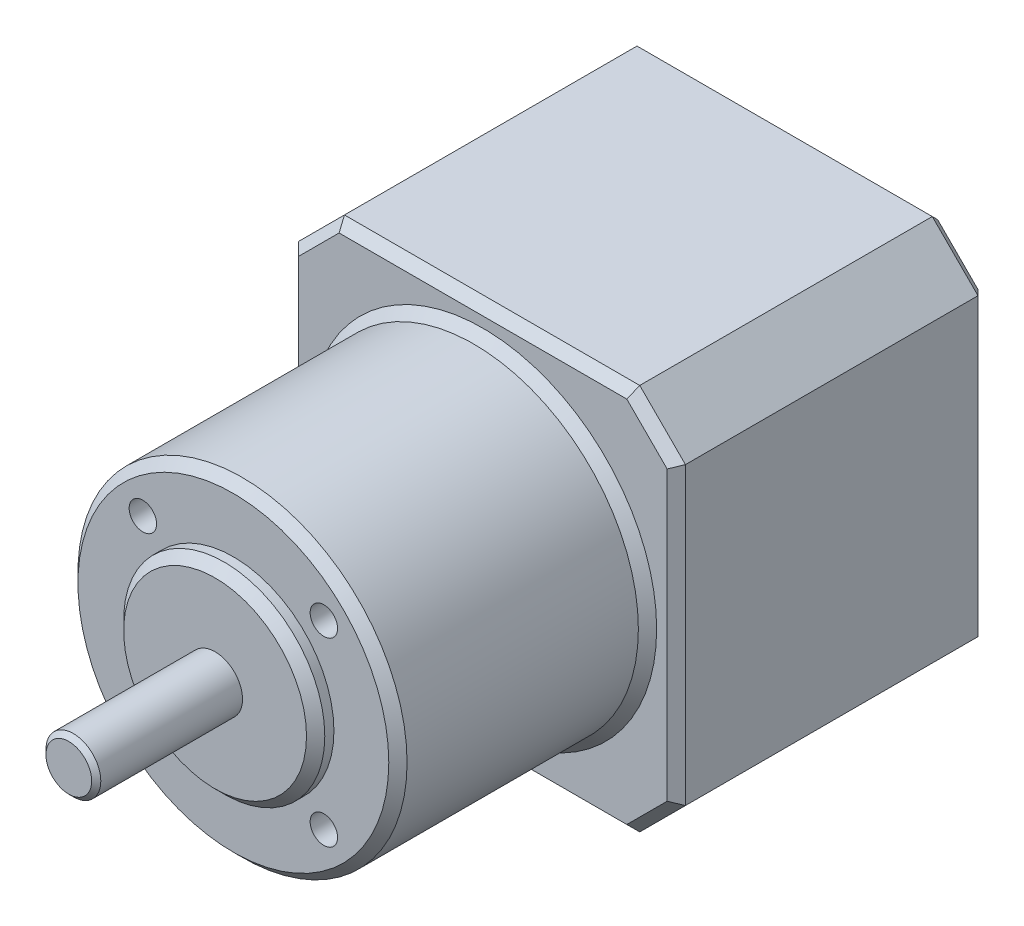
SolidWorks part; units mm, degrees
ref_plane "Front Plane" through (0, 0, 0) normal (0, 0, 1) x (1, 0, 0)
ref_plane "Top Plane" through (0, 0, 0) normal (0, 1, 0) x (1, 0, 0)
ref_plane "Right Plane" through (0, 0, 0) normal (1, 0, 0) x (0, 0, -1)
sketch "Sketch1" plane through (0, 0, 0) normal (0, 0, 1) x (1, 0, 0)
  line L1 (-21.15, 21.15) -> (21.15, 21.15)
  line L2 (-21.15, 21.15) -> (-21.15, -21.15)
  line L3 (-21.15, -21.15) -> (21.15, -21.15)
  line L4 (21.15, 21.15) -> (21.15, -21.15)
  line L5 (-21.15, 21.15) -> (21.15, -21.15) construction
  line L6 (-21.15, -21.15) -> (21.15, 21.15) construction
  point P0 (0, 0)
  dimension "D1" = 42.3
  dimension "D2" = 42.3
extrude "Boss-Extrude1" add sketch "Sketch1" along normal blind 34
chamfer "Chamfer1" distance 5 angle 45 4 edges at (-21.15, -21.15, 17) (-21.15, 21.15, 17) (21.15, -21.15, 17) (21.15, 21.15, 17)
sketch "Sketch2" plane through (0, 0, 34) normal (0, 0, 1) x (1, 0, 0)
  circle A0 centre (0, 0) radius 18
  dimension "D1" = 36
extrude "Boss-Extrude2" add sketch "Sketch2" along normal blind 27.3
sketch "Sketch3" plane through (0, 0, 61.3) normal (0, 0, 1) x (1, 0, 0)
  circle A0 centre (0, 0) radius 11
  dimension "D1" = 22
extrude "Boss-Extrude3" add sketch "Sketch3" along normal blind 2
sketch "Sketch4" plane through (0, 0, 63.3) normal (0, 0, 1) x (1, 0, 0)
  circle A0 centre (0, 0) radius 3
  dimension "D1" = 6
extrude "Boss-Extrude4" add sketch "Sketch4" along normal blind 16
chamfer "Chamfer2" distance 1 angle 45 14 edges at (-18.65, 18.65, 34) (0, 21.15, 34) (21.15, 0, 34) (18.65, -18.65, 34) (0, -21.15, 34) (-18.65, -18.65, 34) (-21.15, 0, 34) (21.15, 0, 0) (18.65, 18.65, 0) (0, 21.15, 0) (-18.65, 18.65, 0) (-21.15, 0, 0) (-18.65, -18.65, 0) (0, -21.15, 0)
chamfer "Chamfer3" distance 0.5 angle 45 1 edges at (3, 0, 79.3)
sketch "Sketch5" plane through (0, 0, 61.3) normal (0, 0, 1) x (1, 0, 0)
  line L0 (0, 0) -> (35.1247, 0) construction
  line L1 (0, 0) -> (25.531, 25.531) construction
  circle A0 centre (9.8995, 9.8995) radius 1.5
  circle A1 centre (9.8995, -9.8995) radius 1.5
  circle A2 centre (-9.8995, -9.8995) radius 1.5
  circle A3 centre (-9.8995, 9.8995) radius 1.5
  point P15 (0, 0)
  dimension "D1" = 3
  dimension "D2" = 45
  dimension "D3" = 14
  dimension "D4" = 4
extrude "Cut-Extrude1" cut sketch "Sketch5" against normal blind 5
